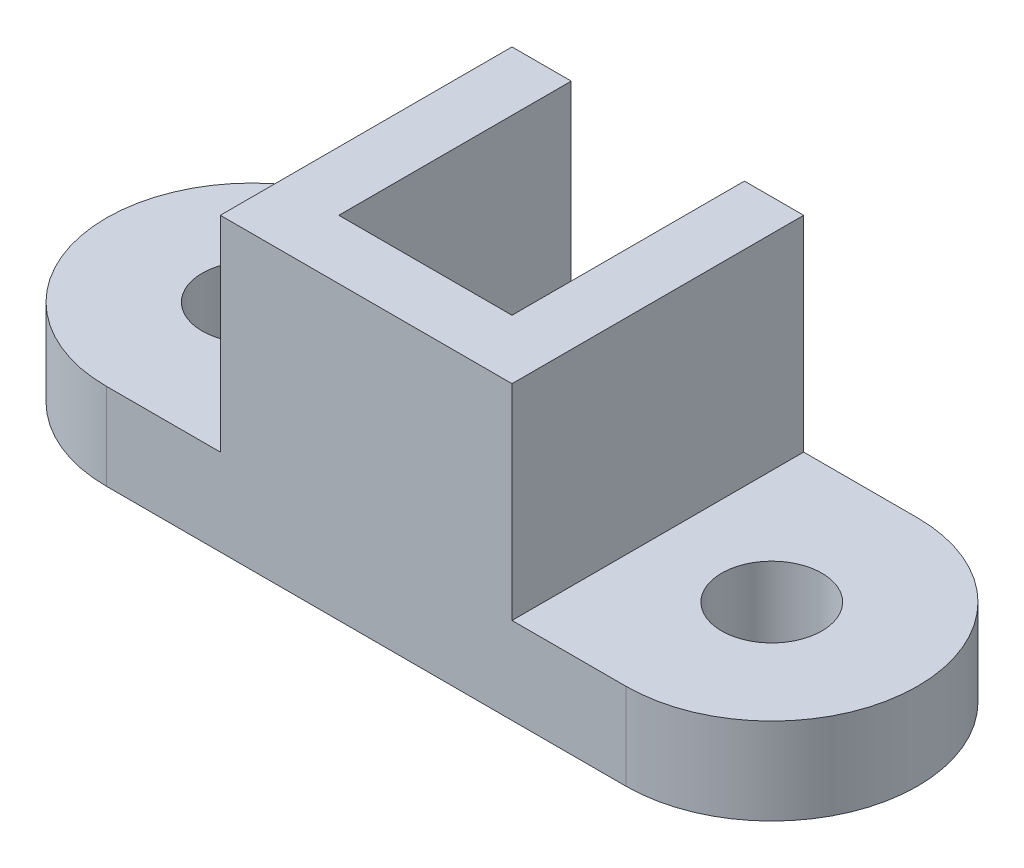
SolidWorks part; units mm, degrees
ref_plane "Front Plane" through (0, 0, 0) normal (0, 0, 1) x (1, 0, 0)
ref_plane "Top Plane" through (0, 0, 0) normal (0, 1, 0) x (1, 0, 0)
ref_plane "Right Plane" through (0, 0, 0) normal (1, 0, 0) x (0, 0, -1)
sketch "Sketch1" plane through (0, 0, 0) normal (0, 1, 0) x (1, 0, 0)
  line L0 (-57, 0) -> (57, 0) construction
  line L1 (-57, 32) -> (57, 32)
  line L2 (-57, -32) -> (57, -32)
  arc A0 (-57, 32) -> (-57, -32) centre (-57, 0) ccw
  arc A1 (57, -32) -> (57, 32) centre (57, 0) ccw
  circle A2 centre (-57, 0) radius 11
  circle A3 centre (57, 0) radius 11
  point P2 (0, 0)
  dimension "D2" = 32
  dimension "D3" = 22
  dimension "D1" = 114
extrude "Boss-Extrude1" add sketch "Sketch1" along normal blind 19
sketch "Sketch2" plane through (0, 19, 0) normal (0, 1, 0) x (1, 0, 0)
  line L0 (57, 32) -> (-57, 32) construction
  line L1 (32, -32) -> (-32, -32)
  line L2 (32, -32) -> (32, 32)
  line L3 (32, 32) -> (-32, 32)
  line L4 (-32, -32) -> (-32, 32)
  line L5 (32, -32) -> (-32, 32) construction
  line L6 (32, 32) -> (-32, -32) construction
  point P0 (0, 0)
  dimension "D1" = 64
extrude "Boss-Extrude2" add sketch "Sketch2" along normal blind 45
ref_plane "Plane3" through (0, 0, 0) normal (1, 0, 0) x (0, 0, -1)
sketch "Sketch5" plane through (0, 0, 0) normal (1, 0, 0) x (0, 0, -1)
  line L3 (-32, 64) -> (32, 64) construction
  line L5 (32, 19) -> (32, 0) construction
  line L6 (-32, 0) -> (32, 0) construction
  line L7 (-19, 64) -> (32, 13)
  line L12 (32, 64) -> (32, 13)
  line L13 (-19, 64) -> (32, 64)
  point P0 (0, 0)
  point P4 (32, 13.5036)
  dimension "D1" = 13
extrude "Cut-Extrude4" cut sketch "Sketch5" against normal mid plane 38
